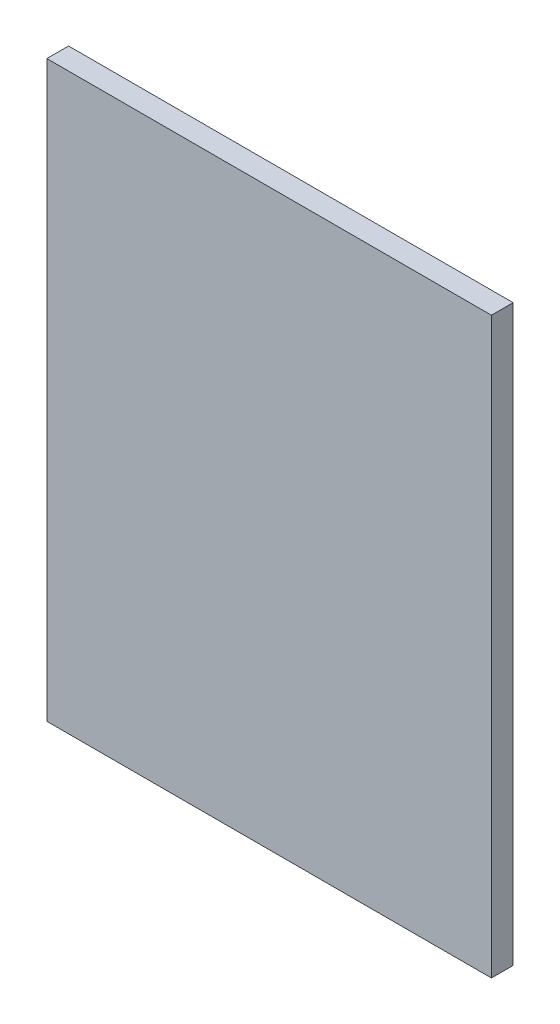
SolidWorks part; units mm, degrees
ref_plane "Front Plane" through (0, 0, 0) normal (0, 0, 1) x (1, 0, 0)
ref_plane "Top Plane" through (0, 0, 0) normal (0, 1, 0) x (1, 0, 0)
ref_plane "Right Plane" through (0, 0, 0) normal (1, 0, 0) x (0, 0, -1)
sketch "Sketch1" plane through (0, 0, 0) normal (0, 0, 1) x (1, 0, 0)
  line L1 (0, 0) -> (57.15, 0)
  line L2 (0, 0) -> (0, -73.787)
  line L3 (0, -73.787) -> (57.15, -73.787)
  line L4 (57.15, 0) -> (57.15, -73.787)
  dimension "D1" = 73.787
  dimension "D2" = 57.15
extrude "Boss-Extrude1" add sketch "Sketch1" along normal blind 2.794
